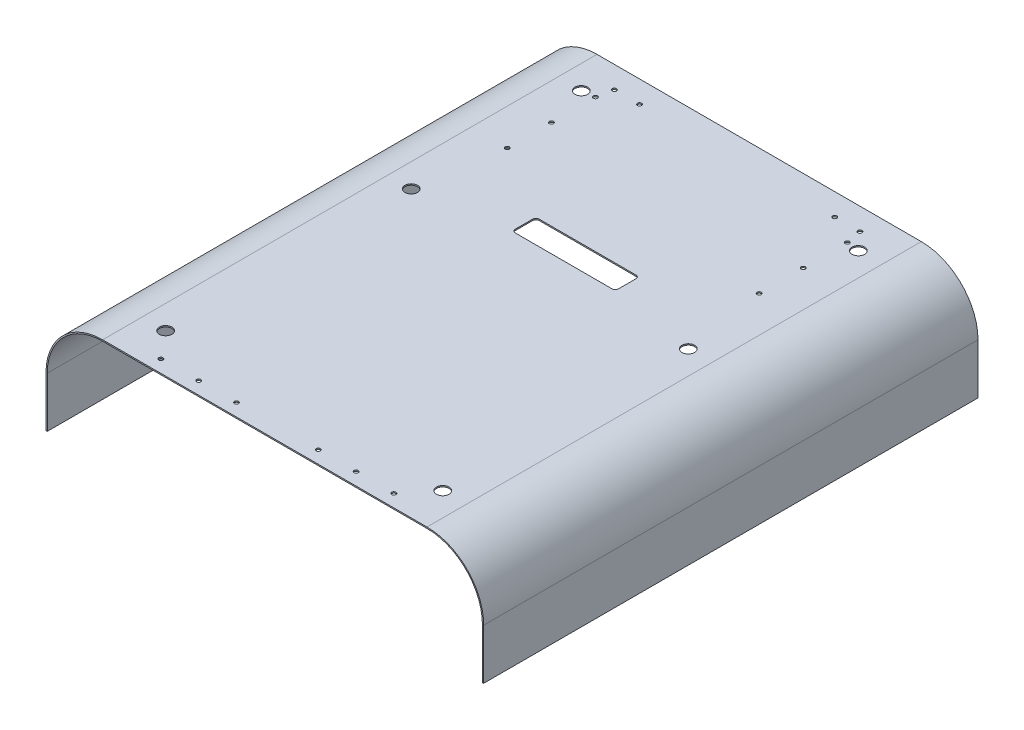
SolidWorks part; units mm, degrees
ref_plane "Front Plane" through (0, 0, 0) normal (0, 0, 1) x (1, 0, 0)
ref_plane "Top Plane" through (0, 0, 0) normal (0, 1, 0) x (1, 0, 0)
ref_plane "Right Plane" through (0, 0, 0) normal (1, 0, 0) x (0, 0, -1)
sketch "Sketch1" plane through (0, 0, 0) normal (0, 0, 1) x (1, 0, 0)
  line L0 (-347.5, -170) -> (-347.5, -90)
  line L1 (-257.5, 0) -> (257.5, 0)
  line L2 (347.5, -90) -> (347.5, -170)
  arc A0 (-347.5, -90) -> (-257.5, 0) centre (-257.5, -90) cw
  arc A1 (257.5, 0) -> (347.5, -90) centre (257.5, -90) cw
  point P4 (0, 0)
  point P8 (-347.5, 0)
  point P11 (347.5, 0)
  dimension "D5" = 90
  dimension "D6" = 90
  dimension "D1" = 695
  dimension "D2" = 170
  dimension "D3" = 170
  dimension "D4" = 0
surface "Surface-Extrude1" sketch "Sketch1" parameters "D1"=785
thicken "Thicken1" surfaces to thicken 101 thickness 2 parameters "D1"=2
sketch "Sketch2" plane through (0, 0, 0) normal (0, 1, 0) x (1, 0, 0)
  line L0 (-257.5, 0) -> (257.5, 0) construction
  circle A0 centre (220, -62.5) radius 10
  dimension "D1" = 20
  dimension "D2" = 62.5
  dimension "D3" = 220
extrude "Cut-Extrude1" cut sketch "Sketch2" against normal through all
ref_plane "Plane1" through (0, 0, 392.5) normal (0, 0, -1) x (-1, 0, 0)
mirror "Mirror1" about plane through (0, 0, 392.5) normal (0, 0, -1) of "Cut-Extrude1"
ref_plane "Plane2" through (0, 0, 0) normal (-1, 0, 0) x (0, 0, 1)
sketch "Sketch3" plane through (0, 0, 0) normal (0, 1, 0) x (1, 0, 0)
  circle A0 centre (220, -332.5) radius 10
  circle A1 centre (220, -62.5) radius 10 construction
  dimension "D1" = 20
  dimension "D3" = 270
  dimension "D2" = 220
extrude "Cut-Extrude2" cut sketch "Sketch3" against normal through all
mirror "Mirror2" about plane through (0, 0, 0) normal (-1, 0, 0) of "Mirror1", "Cut-Extrude2", "Cut-Extrude1"
sketch "Sketch4" plane through (0, 0, 0) normal (0, 1, 0) x (1, 0, 0)
  line L0 (-257.5, 0) -> (257.5, 0) construction
  line L1 (77, -310.5) -> (-77, -310.5)
  line L2 (82, -305.5) -> (82, -277.5)
  line L3 (77, -272.5) -> (-77, -272.5)
  line L4 (-82, -305.5) -> (-82, -277.5)
  line L5 (347.5, 0) -> (347.5, -785) construction
  line L6 (-347.5, 0) -> (-347.5, -785) construction
  arc A0 (-77, -272.5) -> (-82, -277.5) centre (-77, -277.5) ccw
  arc A1 (82, -277.5) -> (77, -272.5) centre (77, -277.5) ccw
  arc A2 (77, -310.5) -> (82, -305.5) centre (77, -305.5) ccw
  arc A3 (-77, -310.5) -> (-82, -305.5) centre (-77, -305.5) cw
  point P18 (82, -310.5)
  dimension "D5" = 5
  dimension "D1" = 310.5
  dimension "D2" = 38
  dimension "D3" = 265.5
  dimension "D4" = 265.5
extrude "Cut-Extrude3" cut sketch "Sketch4" against normal through all
hole_wizard "Ø6.6 (6.6) Diameter Slot1" positions "Sketch5" profile "Sketch6" size "Ø6.6" standard "ISO" slot yes end condition through all
sketch "Sketch5" plane through (0, -2, 0) normal (0, -1, 0) x (-1, 0, 0)
  point P0 (185, -765)
  point P3 (125, -765)
  point P6 (65, -765)
  point P9 (-65, -765)
  point P12 (-125, -765)
  point P15 (-185, -765)
  point P18 (200, -200)
  point P21 (200, -130)
  point P24 (155, -35)
  point P27 (195, -35)
  point P30 (200, -60)
  point P33 (-195, -35)
  point P36 (-155, -35)
  point P39 (-200, -60)
  point P42 (-200, -130)
  point P45 (-200, -200)
sketch "Sketch6" plane through (-185, -2, 765) normal (1, 0, 0) x (0, 0, -1)
  line L0 (0, 0) -> (0, 2)
  line L1 (0, 2) -> (3.3, 2)
  line L2 (3.3, 2) -> (3.3, 0)
  line L5 (3.3, 0) -> (0, 0)
  line L11 (0, -6.35) -> (0, 107.95) construction
  dimension "Thru Hole Dia." = 6.6
  dimension "Thru Hole Depth" = 2
